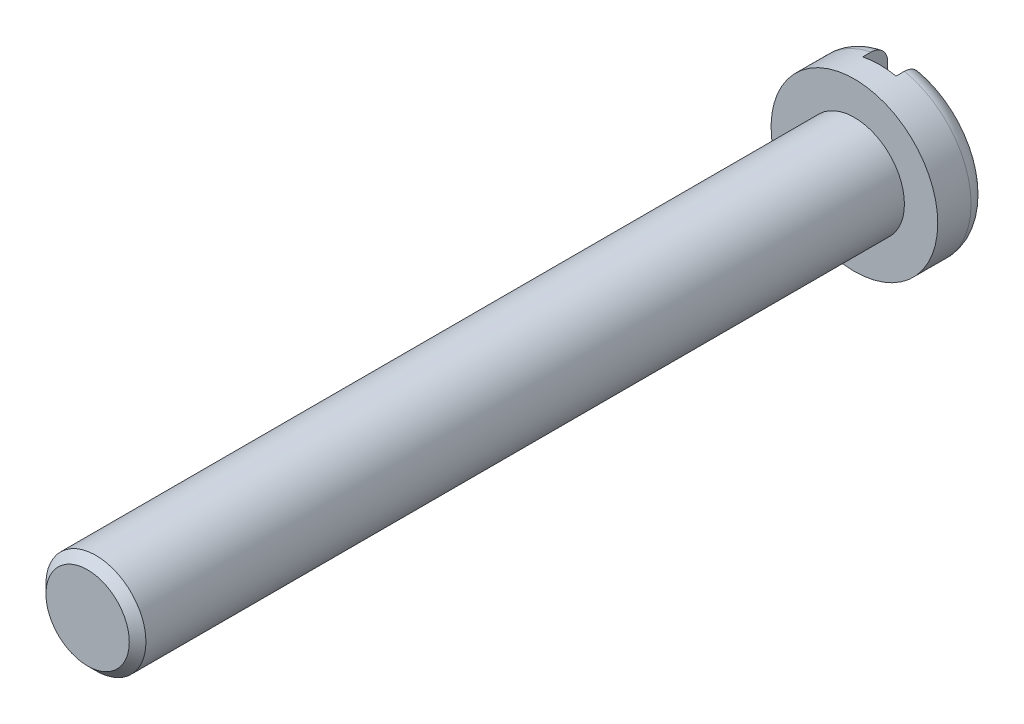
SolidWorks part; units mm, degrees
ref_plane "Plane1" through (0, 0, 0) normal (0, 0, 1) x (1, 0, 0)
ref_plane "Plane2" through (0, 0, 0) normal (0, 1, 0) x (1, 0, 0)
ref_plane "Plane3" through (0, 0, 0) normal (1, 0, 0) x (0, 0, -1)
sketch "Esquisse1" plane through (0, 0, 0) normal (0, 0, 1) x (1, 0, 0)
  circle A0 centre (0, 0) radius 2.5
  dimension "D1" = 5
extrude "Base-Extrusion" add sketch "Esquisse1" along normal blind 1.5
sketch "Esquisse2" plane through (0, 0, 1.5) normal (0, 0, 1) x (1, 0, 0)
  circle A0 centre (0, 0) radius 1.5
  dimension "D1" = 3
extrude "Boss.-Extru.1" add sketch "Esquisse2" along normal blind 23
chamfer "Chanfrein1" distance 0.25 angle 45
sketch "Esquisse3" plane through (0, 0, 0) normal (0, 0, -1) x (-1, 0, 0)
  line L0 (0, 0) -> (0, -4) construction
  line L1 (0.5, 3) -> (0.5, -5)
  line L2 (-0.5, 3) -> (-0.5, -5)
  line L3 (0.5, -5) -> (-0.5, -5)
  line L4 (0.5, 3) -> (-0.5, 3)
  dimension "D1" = 1
extrude "Enlèv. mat.-Extru.1" cut sketch "Esquisse3" against normal blind 0.75
fillet "Congé1" radius 0.5
